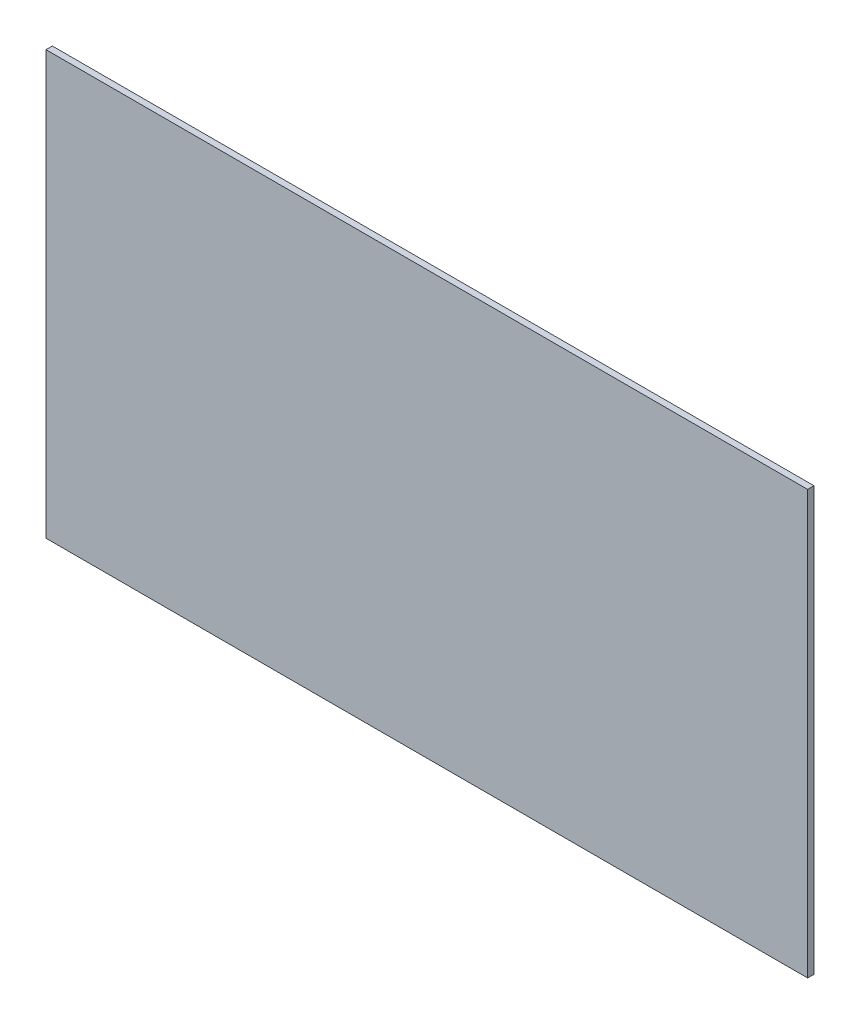
SolidWorks part; units mm, degrees
ref_plane "前基準面" through (0, 0, 0) normal (0, 0, 1) x (1, 0, 0)
ref_plane "上基準面" through (0, 0, 0) normal (0, 1, 0) x (1, 0, 0)
ref_plane "右基準面" through (0, 0, 0) normal (1, 0, 0) x (0, 0, -1)
sketch "草圖1" plane through (0, 0, 0) normal (0, 0, 1) x (1, 0, 0)
  line L1 (-120.7904, 56.4972) -> (59.2096, 56.4972)
  line L2 (-120.7904, 56.4972) -> (-120.7904, -43.5028)
  line L3 (-120.7904, -43.5028) -> (59.2096, -43.5028)
  line L4 (59.2096, 56.4972) -> (59.2096, -43.5028)
  dimension "D1" = 180
  dimension "D2" = 100
extrude "填料-伸長1" add sketch "草圖1" along normal blind 1.5
